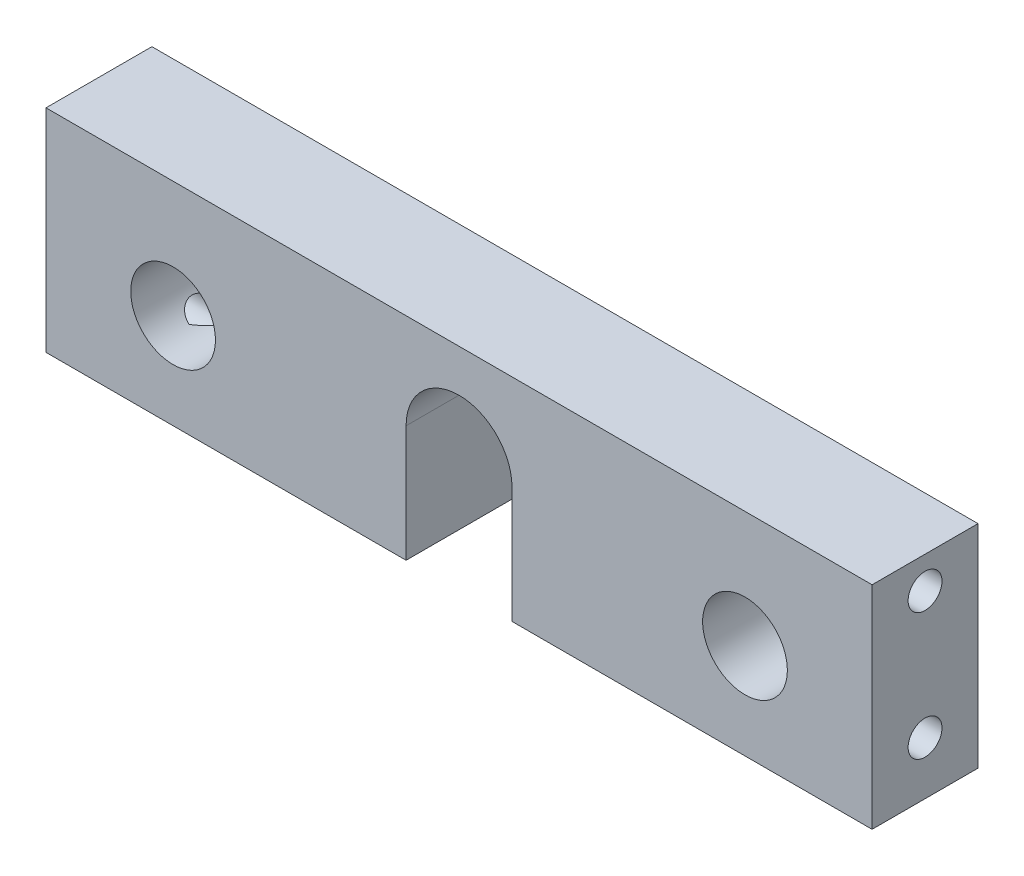
SolidWorks part; units mm, degrees
ref_plane "Front Plane" through (0, 0, 0) normal (0, 0, 1) x (1, 0, 0)
ref_plane "Top Plane" through (0, 0, 0) normal (0, 1, 0) x (1, 0, 0)
ref_plane "Right Plane" through (0, 0, 0) normal (1, 0, 0) x (0, 0, -1)
sketch "Sketch1" plane through (0, 0, 0) normal (1, 0, 0) x (0, 0, -1)
  line L0 (-2.5, 0) -> (2.5, 0)
  line L1 (-2.5, 0) -> (-2.5, 10)
  line L2 (-2.5, 10) -> (2.5, 10)
  line L3 (2.5, 10) -> (2.5, 0)
  dimension "D1" = 5
  dimension "D2" = 10
extrude "Boss-Extrude1" add sketch "Sketch1" along normal blind 39
hole_wizard "Tap Drill for M2x0.4 Tap1" positions "Sketch3" profile "Sketch2" hole size "M2x0.4" standard "ANSI Metric"
sketch "Sketch3" plane through (39, 0, 0) normal (1, 0, 0) x (0, 0, -1)
  line L0 (-2.5, 0) -> (2.5, 0) construction
  point P0 (0, 8.5)
  point P2 (0, 2.5)
  dimension "D1" = 6
  dimension "D2" = 2.5
sketch "Sketch2" plane through (39, 8.5, 0) normal (0, 1, 0) x (0, 0, -1)
  line L0 (0, 0) -> (0, 5.4807)
  line L1 (0, 5.4807) -> (0.8, 5)
  line L2 (0.8, 5) -> (0.8, 0)
  line L5 (0.8, 0) -> (0, 0)
  line L10 (0, 5.4807) -> (-0.8, 5) construction
  line L11 (0, -6.35) -> (0, 107.95) construction
  dimension "Hole Dia." = 1.6
  dimension "Hole Depth" = 5
  dimension "Drill Angle" = 118
hole_wizard "Tap Drill for M2x0.4 Tap2" positions "Sketch5" profile "Sketch4" hole size "M2x0.4" standard "ANSI Metric"
sketch "Sketch5" plane through (0, 0, 0) normal (-1, 0, 0) x (0, 0, 1)
  point P0 (0, 8.5)
  point P2 (0, 2.5)
  dimension "D1" = 2.5
  dimension "D2" = 6
sketch "Sketch4" plane through (0, 8.5, 0) normal (0, 1, 0) x (0, 0, 1)
  line L0 (0, 0) -> (0, 5.4807)
  line L1 (0, 5.4807) -> (0.8, 5)
  line L2 (0.8, 5) -> (0.8, 0)
  line L5 (0.8, 0) -> (0, 0)
  line L10 (0, 5.4807) -> (-0.8, 5) construction
  line L11 (0, -6.35) -> (0, 107.95) construction
  dimension "Hole Dia." = 1.6
  dimension "Hole Depth" = 5
  dimension "Drill Angle" = 118
sketch "Sketch8" plane through (0, 0, 2.5) normal (0, 0, 1) x (1, 0, 0)
  line L0 (17, 0) -> (17, 5.5)
  line L2 (22, 5.5) -> (22, 0)
  line L3 (22, 0) -> (17, 0)
  line L5 (0, 10) -> (0, 0) construction
  line L6 (39, 10) -> (0, 10) construction
  line L7 (39, 10) -> (39, 0) construction
  line L8 (0, 10) -> (0, 0) construction
  line L9 (39, 0) -> (0, 0) construction
  circle A0 centre (6, 4.5) radius 2
  circle A1 centre (33, 4.5) radius 2
  arc A2 (17, 5.5) -> (22, 5.5) centre (19.5, 5.5) cw
  dimension "D1" = 4
  dimension "D2" = 2.5
  dimension "D3" = 19.5
  dimension "D4" = 6
  dimension "D5" = 5.5
  dimension "D6" = 6
  dimension "D7" = 4.5
extrude "Cut-Extrude1" cut sketch "Sketch8" against normal up to next
